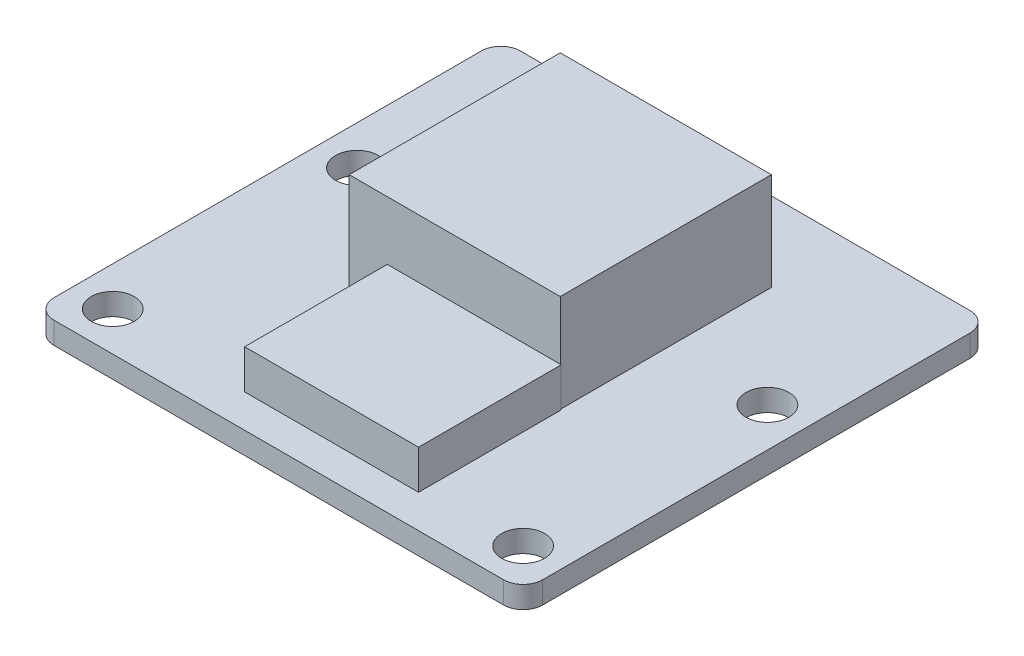
SolidWorks part; units mm, degrees
ref_plane "Front" through (0, 0, 0) normal (0, 0, 1) x (1, 0, 0)
ref_plane "Top" through (0, 0, 0) normal (0, 1, 0) x (1, 0, 0)
ref_plane "Right" through (0, 0, 0) normal (1, 0, 0) x (0, 0, -1)
sketch "Sketch1" plane through (0, 0, 0) normal (0, 1, 0) x (1, 0, 0)
  line L1 (12.5, 11.931) -> (-12.5, 11.931)
  line L2 (12.5, 11.931) -> (12.5, -11.931)
  line L3 (12.5, -11.931) -> (-12.5, -11.931)
  line L4 (-12.5, 11.931) -> (-12.5, -11.931)
  line L5 (12.5, 11.931) -> (-12.5, -11.931) construction
  line L6 (12.5, -11.931) -> (-12.5, 11.931) construction
  point P0 (0, 0)
  dimension "D1" = 23.862
  dimension "D2" = 25
extrude "Boss-Extrude1" add sketch "Sketch1" along normal blind 1.12
fillet "Fillet1" radius 1 4 edges at (-12.5, 0.56, -11.931) (12.5, 0.56, -11.931) (12.5, 0.56, 11.931) (-12.5, 0.56, 11.931)
sketch "Sketch2" plane through (0, 1.12, 0) normal (0, 1, 0) x (1, 0, 0)
  line L0 (-11.5, -11.931) -> (11.5, -11.931) construction
  line L4 (-12.5, 10.931) -> (-12.5, -10.931) construction
  circle A0 centre (-10.5, 2.569) radius 1.1
  circle A1 centre (10.5, 2.569) radius 1.1
  circle A2 centre (-10.5, -9.931) radius 1.1
  circle A3 centre (10.5, -9.931) radius 1.1
  point P2 (0, 0)
  point P16 (0, 0)
  point P17 (0, 0)
  dimension "D1" = 14.5
  dimension "D3" = 2.2
  dimension "D2" = 2
  dimension "D4" = 2
extrude "Cut-Extrude1" cut sketch "Sketch2" against normal blind 2
sketch "Sketch3" plane through (0, 1.12, 0) normal (0, 1, 0) x (1, 0, 0)
  line L0 (12.5, -10.931) -> (12.5, 10.931) construction
  line L1 (-5.4, -2.931) -> (5.4, -2.931)
  line L2 (-5.4, -2.931) -> (-5.4, 7.869)
  line L3 (-5.4, 7.869) -> (5.4, 7.869)
  line L4 (5.4, -2.931) -> (5.4, 7.869)
  line L5 (-5.4, -2.931) -> (5.4, 7.869) construction
  line L6 (-5.4, 7.869) -> (5.4, -2.931) construction
  line L7 (-11.5, -11.931) -> (11.5, -11.931) construction
  point P0 (0, 2.469)
  dimension "D1" = 10.8
  dimension "D2" = 10.8
  dimension "D3" = 12.5
  dimension "D4" = 14.4
extrude "Boss-Extrude2" add sketch "Sketch3" along normal blind 5
sketch "Sketch4" plane through (0, 1.12, 0) normal (0, 1, 0) x (1, 0, 0)
  line L0 (-5.4, -2.931) -> (5.4, -2.931) construction
  line L1 (-3.45, -10.231) -> (5.45, -10.231)
  line L2 (-3.45, -10.231) -> (-3.45, -2.931)
  line L3 (-3.45, -2.931) -> (5.45, -2.931)
  line L4 (5.45, -10.231) -> (5.45, -2.931)
  line L5 (-3.45, -10.231) -> (5.45, -2.931) construction
  line L6 (-3.45, -2.931) -> (5.45, -10.231) construction
  point P0 (1, -6.581)
  point P7 (-4.3451, -9.4396)
  point P8 (6.6753, -10.1438)
  dimension "D1" = 8.9
  dimension "D2" = 7.3
  dimension "D3" = 1
extrude "Boss-Extrude3" add sketch "Sketch4" along normal blind 2
